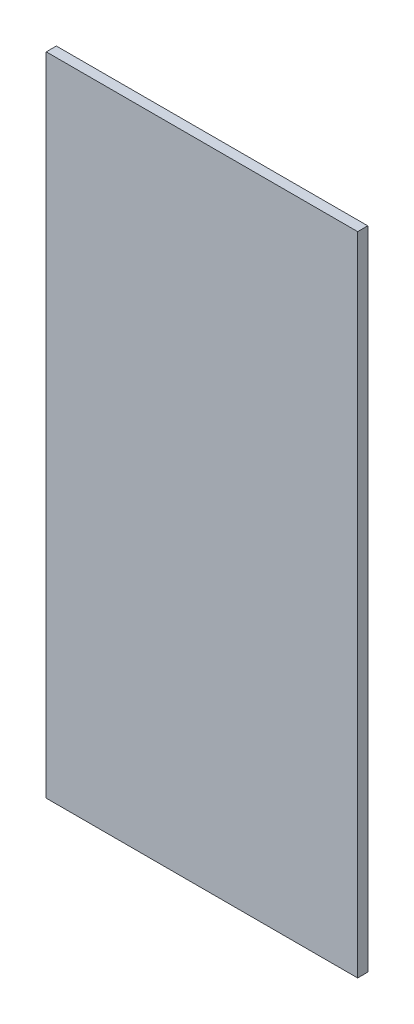
SolidWorks part; units mm, degrees
material "Vidro"
ref_plane "Plano frontal" through (0, 0, 0) normal (0, 0, 1) x (1, 0, 0)
ref_plane "Plano superior" through (0, 0, 0) normal (0, 1, 0) x (1, 0, 0)
ref_plane "Plano direito" through (0, 0, 0) normal (1, 0, 0) x (0, 0, -1)
sketch "Esboço1" plane through (0, 0, 0) normal (0, 0, 1) x (1, 0, 0)
  line L1 (92.5, -192) -> (-92.5, -192)
  line L2 (92.5, -192) -> (92.5, 192)
  line L3 (92.5, 192) -> (-92.5, 192)
  line L4 (-92.5, -192) -> (-92.5, 192)
  line L5 (92.5, -192) -> (-92.5, 192) construction
  line L6 (92.5, 192) -> (-92.5, -192) construction
  point P0 (0, 0)
  point P5 (0, 0)
  dimension "D1" = 185
  dimension "D2" = 384
extrude "Ressalto-extrusão1" add sketch "Esboço1" along normal blind 6
